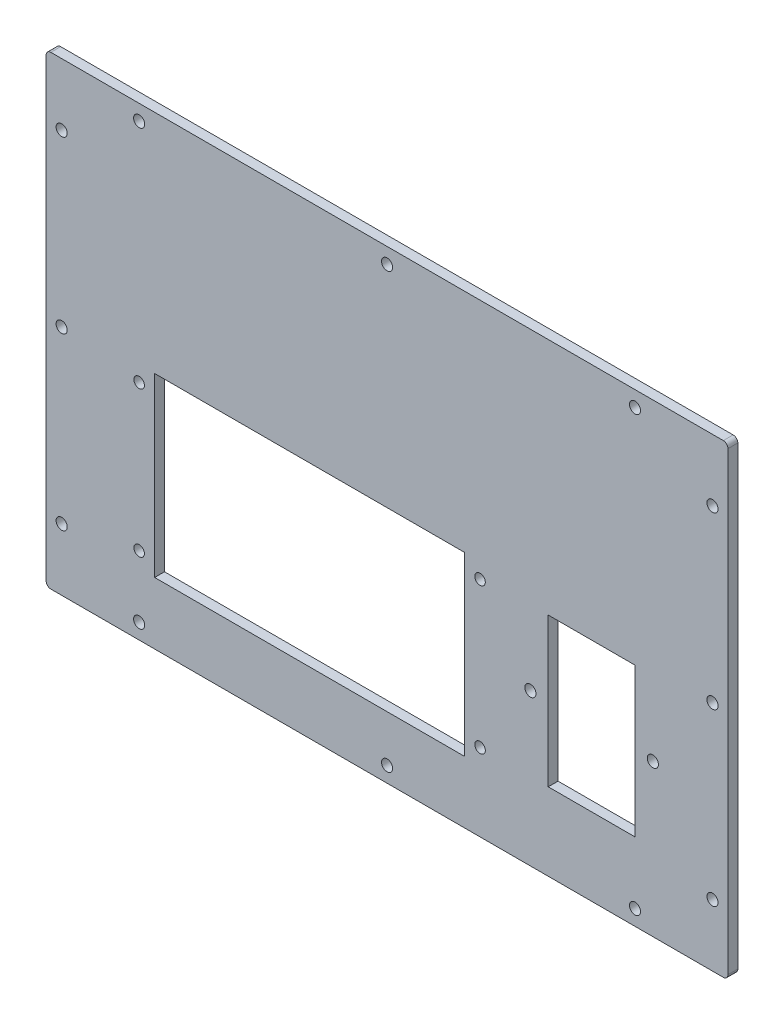
SolidWorks part; units mm, degrees
ref_plane "Front Plane" through (0, 0, 0) normal (0, 0, 1) x (1, 0, 0)
ref_plane "Top Plane" through (0, 0, 0) normal (0, 1, 0) x (1, 0, 0)
ref_plane "Right Plane" through (0, 0, 0) normal (1, 0, 0) x (0, 0, -1)
sketch "Sketch1" plane through (0, 0, 0) normal (0, 0, 1) x (1, 0, 0)
  line L0 (0, 0) -> (0, 75) construction
  line L1 (-110, -75) -> (110, -75)
  line L2 (-110, -75) -> (-110, 75)
  line L3 (-110, 75) -> (110, 75)
  line L4 (110, -75) -> (110, 75)
  line L5 (-110, -75) -> (110, 75) construction
  line L6 (-110, 75) -> (110, -75) construction
  line L15 (0, 0) -> (-110, 0) construction
  point P0 (0, 0)
  dimension "D1" = 220
  dimension "D2" = 150
extrude "Boss-Extrude1" add sketch "Sketch1" along normal blind 3.175
hole_wizard "M3 Clearance Hole1" positions "Sketch2" profile "Sketch3" hole size "M3" standard "ANSI Metric" end condition through all
sketch "Sketch2" plane through (0, 0, 3.175) normal (0, 0, 1) x (1, 0, 0)
  line L1 (-105, -70) -> (105, -70)
  line L2 (-105, -70) -> (-105, 70)
  line L3 (-105, 70) -> (105, 70)
  line L4 (105, -70) -> (105, 70)
  line L5 (-105, -70) -> (105, 70) construction
  line L6 (-105, 70) -> (105, -70) construction
  line L7 (-110, -75) -> (-110, 75) construction
  line L8 (-110, 75) -> (110, 75) construction
  point P2 (0, 0)
  point P113 (-80, 70)
  point P115 (80, 70)
  point P116 (0, 70)
  point P118 (-105, 55)
  point P120 (-105, 0)
  point P122 (-105, -55)
  point P124 (-80, -70)
  point P126 (0, -70)
  point P128 (80, -70)
  point P130 (105, -55)
  point P132 (105, 0)
  point P134 (105, 55)
  dimension "D1" = 5
  dimension "D2" = 5
  dimension "D3" = 80
  dimension "D4" = 80
  dimension "D5" = 55
  dimension "D6" = 55
sketch "Sketch3" plane through (0, 0, 3.175) normal (1, 0, 0) x (0, -1, 0)
  line L0 (0, 0) -> (0, 3.175)
  line L1 (0, 3.175) -> (1.8, 3.175)
  line L2 (1.8, 3.175) -> (1.8, 0)
  line L5 (1.8, 0) -> (0, 0)
  line L11 (0, -6.35) -> (0, 107.95) construction
  dimension "Thru Hole Dia." = 3.6
  dimension "Thru Hole Depth" = 3.175
sketch "Sketch4" plane through (0, 0, 3.175) normal (0, 0, 1) x (1, 0, 0)
  line L1 (-5, -5) -> (5, -5)
  line L2 (-5, -5) -> (-5, 5)
  line L3 (-5, 5) -> (5, 5)
  line L4 (5, -5) -> (5, 5)
  line L5 (-5, -5) -> (5, 5) construction
  line L6 (-5, 5) -> (5, -5) construction
  point P0 (0, 0)
  dimension "D1" = 10
  dimension "D2" = 10
extrude "Boss-Extrude2" add sketch "Sketch4" against normal through all
fillet "Fillet2" radius 1.5 4 edges at (-110, -75, 1.5875) (110, -75, 1.5875) (110, 75, 1.5875) (-110, 75, 1.5875)
sketch "Sketch5" plane through (0, 0, 3.175) normal (0, 0, 1) x (1, 0, 0)
  line L0 (46.25, -26) -> (85.75, -26) construction
  line L1 (52, -50) -> (80, -50)
  line L2 (52, -50) -> (52, -2)
  line L3 (52, -2) -> (80, -2)
  line L4 (80, -50) -> (80, -2)
  line L5 (52, -50) -> (80, -2) construction
  line L6 (52, -2) -> (80, -50) construction
  line L7 (-108.5, -75) -> (108.5, -75) construction
  line L8 (110, -73.5) -> (110, 73.5) construction
  line L10 (-90, -60) -> (30, -60)
  line L11 (-90, -60) -> (-90, 60)
  line L12 (-90, 60) -> (30, 60)
  line L13 (30, -60) -> (30, 60)
  line L14 (-90, -60) -> (30, 60) construction
  line L15 (-90, 60) -> (30, -60) construction
  line L16 (-110, -73.5) -> (-110, 73.5) construction
  point P0 (66, -26)
  point P8 (66, -26)
  point P12 (-30, 0)
  dimension "D1" = 28
  dimension "D2" = 48
  dimension "D3" = 39.5
  dimension "D4" = 25
  dimension "D5" = 30
  dimension "D6" = 120
  dimension "D7" = 120
  dimension "D8" = 15
  dimension "D9" = 20
extrude "Cut-Extrude1" cut sketch "Sketch5" against normal through all contours L1 L4 L3 L2 | L11 L10 L13 L12
hole_wizard "M3 Clearance Hole2" positions "Sketch6" profile "Sketch7" hole size "M3" standard "ANSI Metric" end condition through all
sketch "Sketch6" plane through (0, 0, 3.175) normal (0, 0, 1) x (1, 0, 0)
  point P0 (46.25, -26)
  point P3 (85.75, -26)
sketch "Sketch7" plane through (46.25, -26, 3.175) normal (1, 0, 0) x (0, -1, 0)
  line L0 (0, 0) -> (0, 3.175)
  line L1 (0, 3.175) -> (1.8, 3.175)
  line L2 (1.8, 3.175) -> (1.8, 0)
  line L5 (1.8, 0) -> (0, 0)
  line L11 (0, -6.35) -> (0, 107.95) construction
  dimension "Thru Hole Dia." = 3.6
  dimension "Thru Hole Depth" = 3.175
sketch "Sketch8" plane through (0, 0, 3.175) normal (0, 0, 1) x (1, 0, 0)
  line L0 (-110, -73.5) -> (-110, 73.5) construction
  line L1 (-75, 2) -> (25, 2)
  line L2 (-75, 2) -> (-75, -55)
  line L3 (-75, -55) -> (25, -55)
  line L4 (25, 2) -> (25, -55)
  line L5 (-108.5, -75) -> (108.5, -75) construction
  dimension "D1" = 57
  dimension "D2" = 100
  dimension "D3" = 35
  dimension "D4" = 20
extrude "Cut-Extrude2" cut sketch "Sketch8" against normal through all
hole_wizard "M3 Clearance Hole3" positions "Sketch9" profile "Sketch10" hole size "M3" standard "ANSI Metric" end condition through all
sketch "Sketch9" plane through (0, 0, 3.175) normal (0, 0, 1) x (1, 0, 0)
  line L0 (-80, -3) -> (-80, -50) construction
  line L2 (30, -3) -> (30, -50) construction
  line L4 (-75, 2) -> (-75, -55) construction
  line L5 (25, -55) -> (25, 2) construction
  line L6 (25, 2) -> (-75, 2) construction
  point P0 (-80, -3)
  point P2 (-80, -50)
  point P4 (30, -50)
  point P6 (30, -3)
  point P21 (-80, -26.5)
  point P24 (-75, -26.5)
  dimension "D1" = 5
  dimension "D2" = 5
  dimension "D3" = 5
sketch "Sketch10" plane through (-80, -3, 3.175) normal (1, 0, 0) x (0, -1, 0)
  line L0 (0, 0) -> (0, 3.175)
  line L1 (0, 3.175) -> (1.7, 3.175)
  line L2 (1.7, 3.175) -> (1.7, 0)
  line L5 (1.7, 0) -> (0, 0)
  line L11 (0, -6.35) -> (0, 107.95) construction
  dimension "Thru Hole Dia." = 3.4
  dimension "Thru Hole Depth" = 3.175
